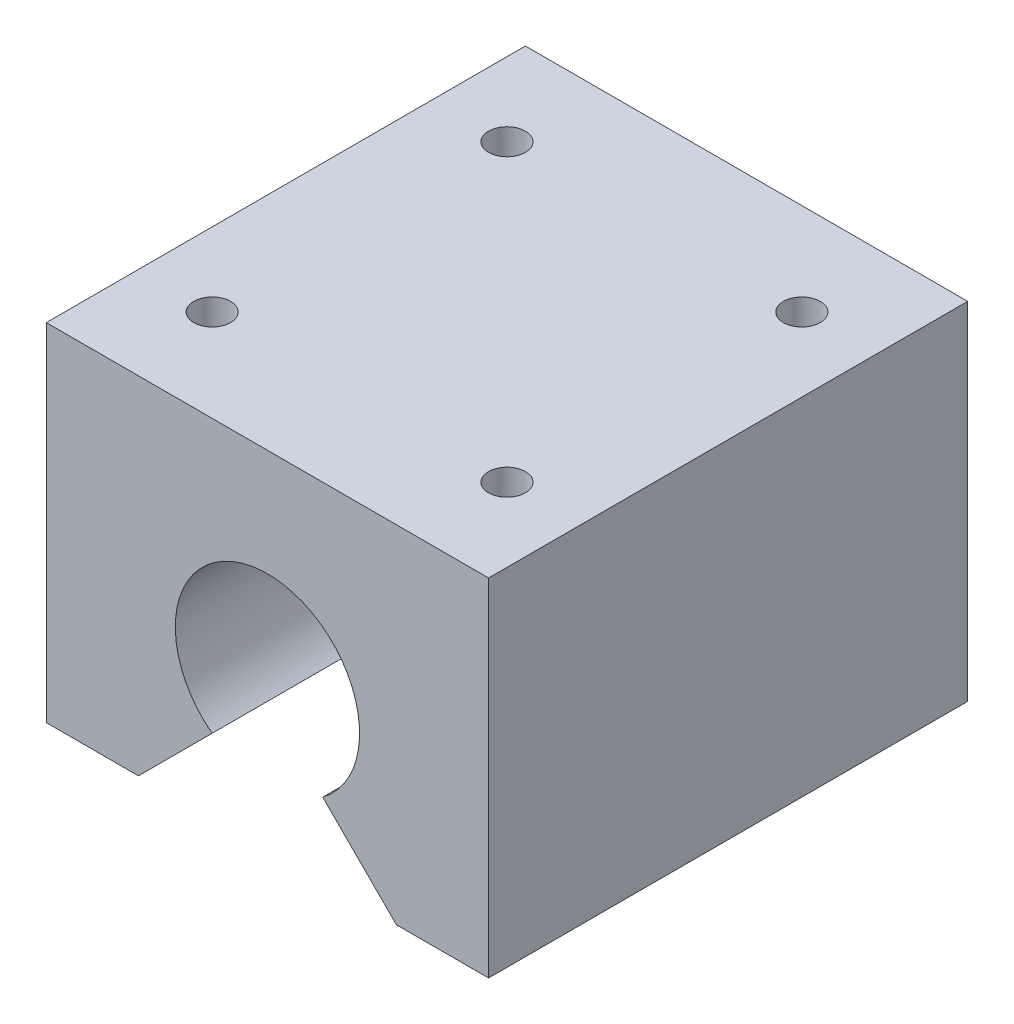
SolidWorks part; units mm, degrees
material "45"
ref_plane "前视基准面" through (0, 0, 0) normal (0, 0, 1) x (1, 0, 0)
ref_plane "上视基准面" through (0, 0, 0) normal (0, 1, 0) x (1, 0, 0)
ref_plane "右视基准面" through (0, 0, 0) normal (1, 0, 0) x (0, 0, -1)
sketch "草图1" plane through (0, 0, 0) normal (0, 0, 1) x (1, 0, 0)
  line L0 (0, 79.5) -> (0, -51) construction
  line L1 (-117.5428, 0) -> (109.8144, 0) construction
  line L2 (-17.5, 0) -> (-7.5, 10)
  line L3 (-30, 47) -> (30, 47)
  line L4 (-30, 47) -> (-30, 0)
  line L5 (-30, 0) -> (-17.5, 0)
  line L6 (30, 47) -> (30, 0)
  line L7 (-30, 47) -> (30, 0) construction
  line L8 (-30, 0) -> (30, 47) construction
  line L9 (17.5, 0) -> (7.5, 10)
  line L10 (17.5, 0) -> (30, 0)
  arc A0 (7.5, 10) -> (-7.5, 10) centre (0, 20) ccw
  point P5 (0, 23.5)
  dimension "D3" = 25
  dimension "D4" = 27
  dimension "D1" = 47
  dimension "D2" = 60
  dimension "D5" = 35
  dimension "D6" = 45
extrude "凸台-拉伸1" add sketch "草图1" along normal mid plane 65
sketch "草图2" plane through (0, 47, 0) normal (0, 1, 0) x (1, 0, 0)
  line L0 (0, 52.4144) -> (0, -36.901) construction
  line L1 (-62.6563, 0) -> (78.6216, 0) construction
  line L3 (-20, -20) -> (20, -20) construction
  line L4 (-20, -20) -> (-20, 20) construction
  line L5 (-20, 20) -> (20, 20) construction
  line L6 (20, -20) -> (20, 20) construction
  line L7 (-20, -20) -> (20, 20) construction
  line L8 (-20, 20) -> (20, -20) construction
  point P5 (0, 0)
  dimension "D1" = 40
  dimension "D2" = 40
hole_wizard "M6 螺纹孔1" positions "3D草图1" profile "草图4" tap size "M6" standard "GB"
sketch3d "3D草图1"
  point P0 (-20, 47, -20)
  point P5 (20, 47, -20)
  point P8 (20, 47, 20)
  point P11 (-20, 47, 20)
sketch "草图4" plane through (-20, 47, -20) normal (1, 0, 0) x (0, 0, 1)
  line L0 (0, 0) -> (0, 11.5022)
  line L1 (0, 11.5022) -> (2.5, 10)
  line L2 (2.5, 10) -> (2.5, 0)
  line L5 (2.5, 0) -> (0, 0)
  line L10 (0, 11.5022) -> (-2.5, 10) construction
  line L11 (0, -6.35) -> (0, 107.95) construction
  dimension "螺纹孔钻头直径" = 5
  dimension "螺纹孔钻头深度" = 10
  dimension "导头角度" = 118
cosmetic thread "孔螺蚊线1" parameters "D1"=10, "D2"=6
cosmetic thread "孔螺蚊线2" parameters "D1"=10, "D2"=6
cosmetic thread "孔螺蚊线3" parameters "D1"=10, "D2"=6
cosmetic thread "孔螺蚊线4" parameters "D1"=10, "D2"=6
